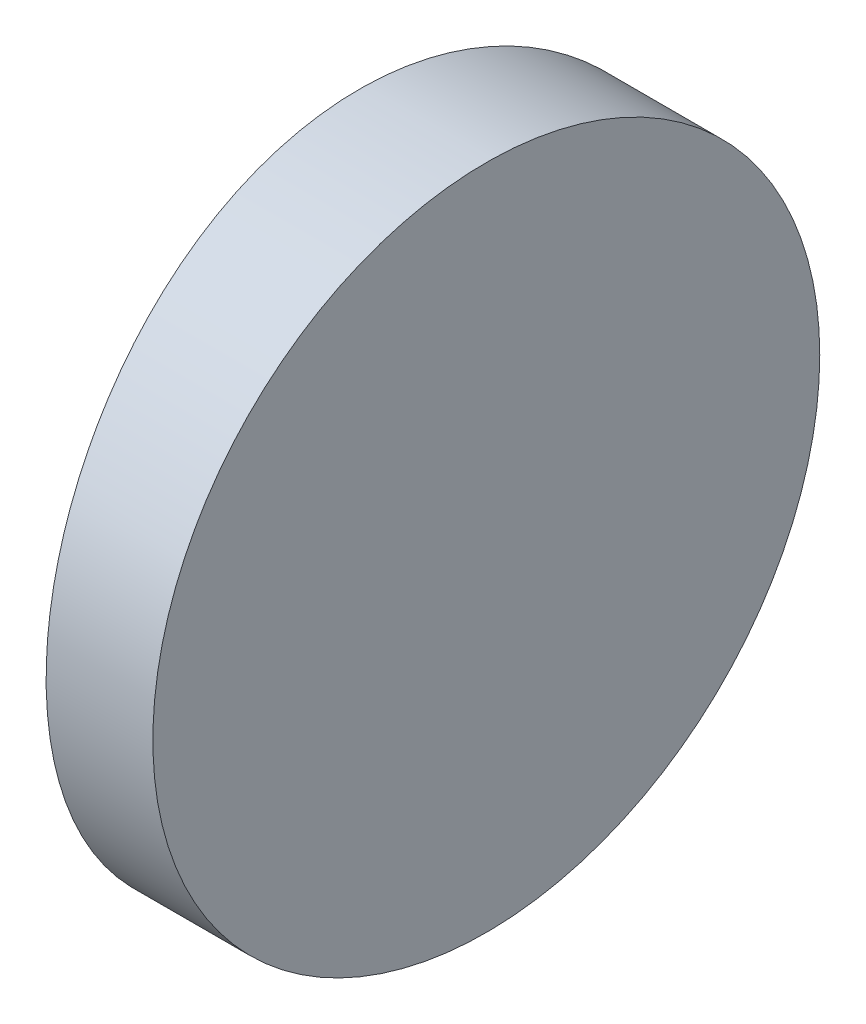
SolidWorks part; units mm, degrees
ref_plane "前视基准面" through (0, 0, 0) normal (0, 0, 1) x (1, 0, 0)
ref_plane "上视基准面" through (0, 0, 0) normal (0, 1, 0) x (1, 0, 0)
ref_plane "右视基准面" through (0, 0, 0) normal (1, 0, 0) x (0, 0, -1)
sketch "草图1" plane through (0, 0, 0) normal (0, 1, 0) x (1, 0, 0)
  line L0 (10.7432, 0) -> (-55.502, 0) construction
  line L1 (-46.9455, 6.25) -> (-44.9448, 6.25)
  line L2 (-46.9455, -6.25) -> (-44.9448, -6.25)
  line L3 (-44.9448, 6.25) -> (-44.9448, -6.25)
  arc A0 (-46.9455, 6.25) -> (-46.9455, -6.25) centre (4.3552, 0) ccw
  point P2 (-55.502, 0)
  point P19 (-47.3248, 0)
  point P20 (-44.9448, 0)
  dimension "D2" = 6.25
  dimension "D3" = 51.68
  dimension "D4" = 2.38
  dimension "D1" = 6.25
extrude "凸台-拉伸1" add sketch "草图1" along normal blind 12.5 contours A0 L2 L3 L1
sketch "草图2" plane through (-44.9448, 0, 0) normal (1, 0, 0) x (0, 0, -1)
  line L0 (6.25, 0) -> (-6.25, 0) construction
  line L7 (-6.25, 0) -> (6.25, 0)
  line L8 (6.25, 0) -> (6.25, 12.5)
  line L9 (6.25, 12.5) -> (-6.25, 12.5)
  line L10 (-6.25, 12.5) -> (-6.25, 0)
  line L11 (-6.25, 0) -> (6.25, 0)
  line L12 (6.25, 0) -> (6.25, 12.5)
  line L13 (6.25, 12.5) -> (-6.25, 12.5)
  line L14 (-6.25, 12.5) -> (-6.25, 0)
  circle A0 centre (0, 6.25) radius 6.25
  line M1 (-6.25, 0) -> (6.25, 0)
  line M2 (6.25, 0) -> (6.25, 12.5)
  line M3 (6.25, 12.5) -> (-6.25, 12.5)
  line M4 (-6.25, 12.5) -> (-6.25, 0)
  dimension "D1" = 12.5
  dimension "D2" = 6.25
  dimension "D3" = 0
extrude "切除-拉伸8" cut sketch "草图2" against normal blind 12.7 contours A0 L13 M4 | A0 L12 M3 | A0 L11 M2 | A0 L14 M1
